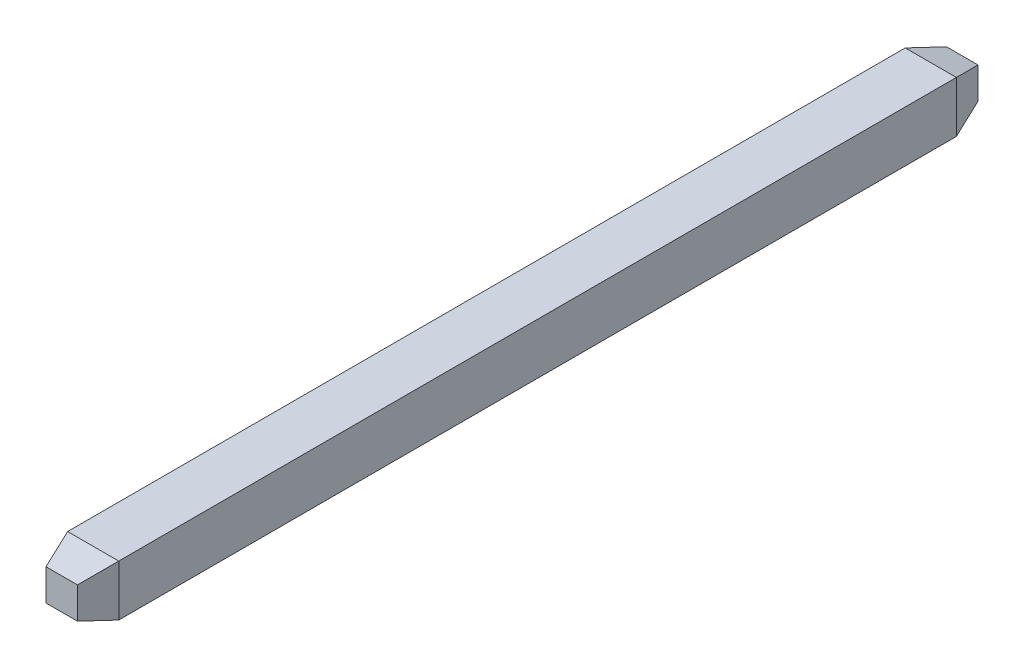
SolidWorks part; units mm, degrees
material "Bronze phosphoreux 10% D, UNS C52400"
ref_plane "Face" through (0, 0, 0) normal (0, 0, 1) x (1, 0, 0)
ref_plane "Dessus" through (0, 0, 0) normal (0, 1, 0) x (1, 0, 0)
ref_plane "Droite" through (0, 0, 0) normal (1, 0, 0) x (0, 0, -1)
sketch "Esquisse1" plane through (0, 0, 0) normal (0, 0, 1) x (1, 0, 0)
  line L1 (-0.325, -0.325) -> (0.325, -0.325)
  line L2 (-0.325, -0.325) -> (-0.325, 0.325)
  line L3 (-0.325, 0.325) -> (0.325, 0.325)
  line L4 (0.325, -0.325) -> (0.325, 0.325)
  line L5 (-0.325, -0.325) -> (0.325, 0.325) construction
  line L6 (-0.325, 0.325) -> (0.325, -0.325) construction
  point P0 (0, 0)
  dimension "D1" = 0.65
extrude "Boss.-Extru.1" add sketch "Esquisse1" along normal blind 6 and the other way blind 5.45
chamfer "Chanfrein1" distance 0.4 distance2 0.125 4 edges at (-0.325, 0, 6) (0, 0.325, 6) (0.325, 0, 6) (0, -0.325, 6)
chamfer "Chanfrein2" distance 0.125 distance2 0.4 4 edges at (0.325, 0, -5.45) (0, -0.325, -5.45) (-0.325, 0, -5.45) (0, 0.325, -5.45)
